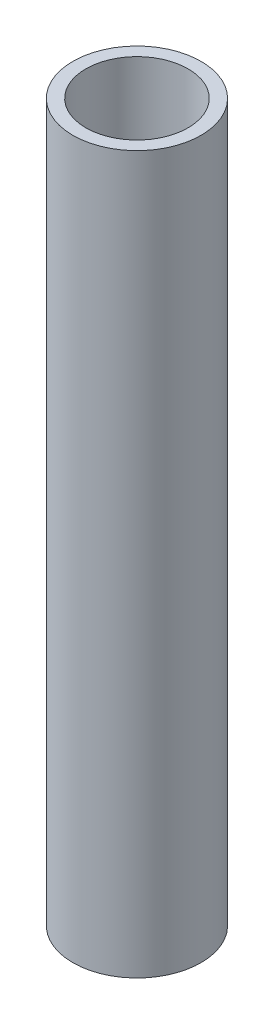
SolidWorks part; units mm, degrees
material "Alloy Steel"
ref_plane "Front Plane" through (0, 0, 0) normal (0, 0, 1) x (1, 0, 0)
ref_plane "Top Plane" through (0, 0, 0) normal (0, 1, 0) x (1, 0, 0)
ref_plane "Right Plane" through (0, 0, 0) normal (1, 0, 0) x (0, 0, -1)
sketch "Sketch1" plane through (0, 0, 0) normal (0, 1, 0) x (1, 0, 0)
  circle A0 centre (0, 0) radius 16.7005
  circle A1 centre (0, 0) radius 13.3223
  dimension "D1" = 33.401
  dimension "D2" = 26.6446
extrude "Boss-Extrude1" add sketch "Sketch1" along normal blind 186.69
